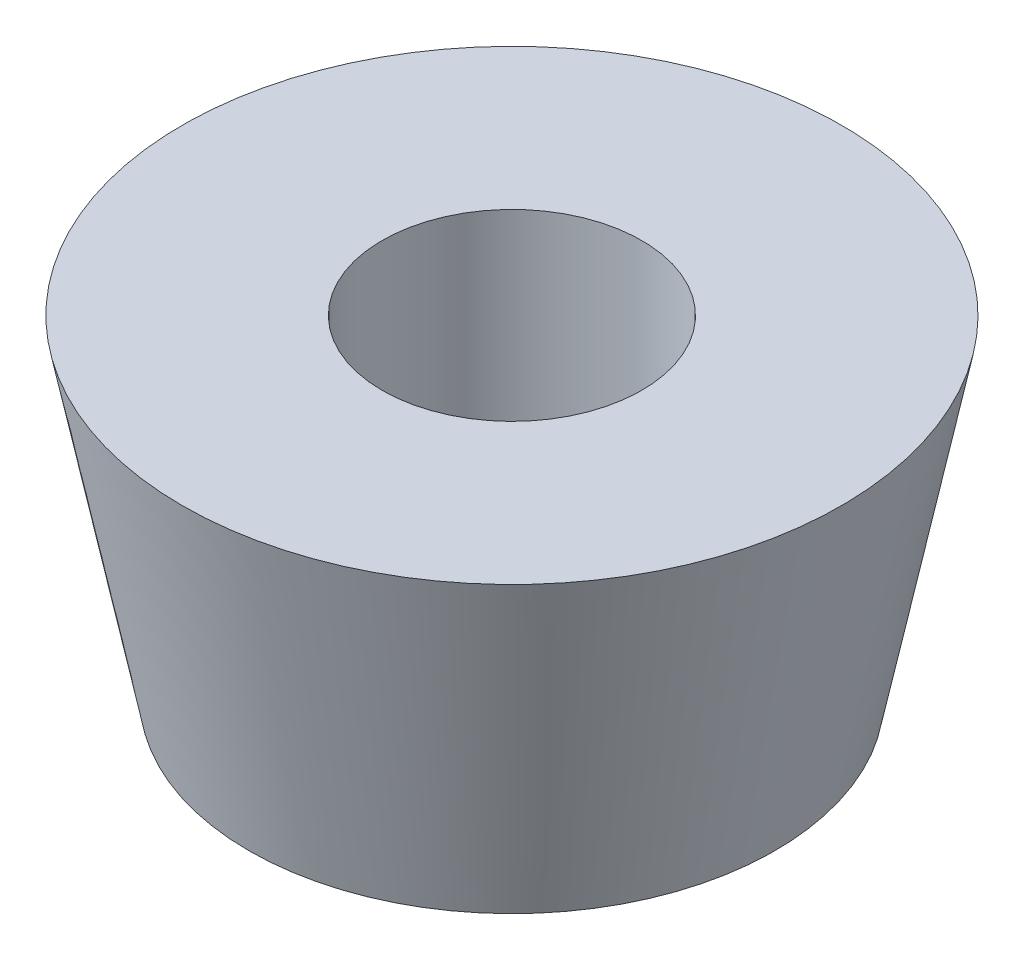
SolidWorks part; units mm, degrees
ref_plane "Front Plane" through (0, 0, 0) normal (0, 0, 1) x (1, 0, 0)
ref_plane "Top Plane" through (0, 0, 0) normal (0, 1, 0) x (1, 0, 0)
ref_plane "Right Plane" through (0, 0, 0) normal (1, 0, 0) x (0, 0, -1)
sketch "Sketch1" plane through (0, 0, 0) normal (0, 0, 1) x (1, 0, 0)
  line L0 (0, 0) -> (0, -5) construction
  line L1 (1.95, 0) -> (1.95, -4.9888)
  line L2 (1.95, -4.9888) -> (3.95, -4.9888)
  line L3 (3.95, -4.9888) -> (4.95, 0)
  line L4 (4.95, 0) -> (1.95, 0)
  dimension "D1" = 5
  dimension "D2" = 3.9
  dimension "D3" = 3
  dimension "D4" = 2
revolve "Revolve1" add sketch "Sketch1" angle 360 about L0
